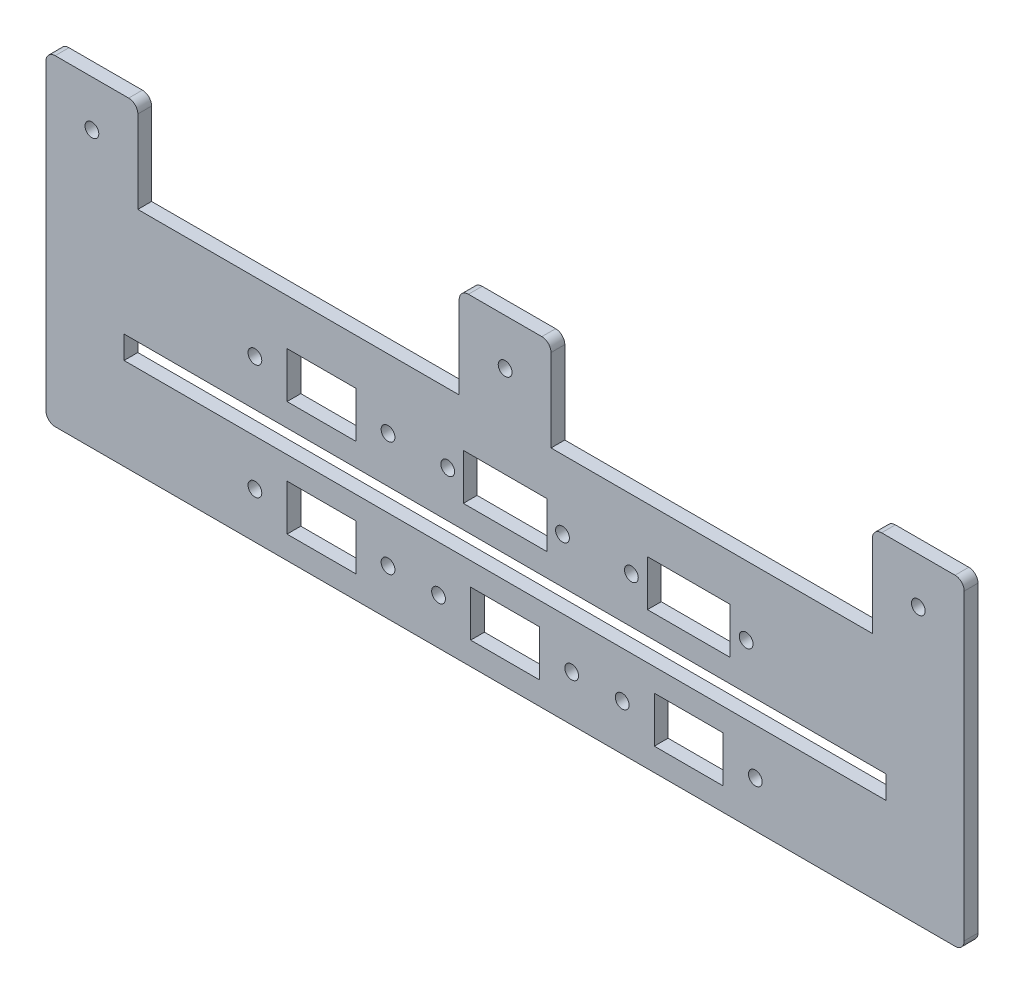
SolidWorks part; units mm, degrees
material "ｱｸﾘﾙ (中-上級の耐衝撃性)"
ref_plane "正面" through (0, 0, 0) normal (0, 0, 1) x (1, 0, 0)
ref_plane "平面" through (0, 0, 0) normal (0, 1, 0) x (1, 0, 0)
ref_plane "右側面" through (0, 0, 0) normal (1, 0, 0) x (0, 0, -1)
sketch "ｽｹｯﾁ1" plane through (0, 0, 0) normal (0, 0, 1) x (1, 0, 0)
  line L1 (-100, 35) -> (100, 35)
  line L2 (-100, 35) -> (-100, -35)
  line L3 (-100, -35) -> (100, -35)
  line L4 (100, 35) -> (100, -35)
  line L5 (-100, 35) -> (100, -35) construction
  line L6 (-100, -35) -> (100, 35) construction
  point P0 (0, 0)
  dimension "D1" = 200
  dimension "D2" = 70
extrude "ﾎﾞｽ - 押し出し1" add sketch "ｽｹｯﾁ1" along normal blind 3
sketch "ｽｹｯﾁ2" plane through (0, 0, 3) normal (0, 0, 1) x (1, 0, 0)
  line L0 (-100, 35) -> (-80, 35)
  line L1 (100, 35) -> (-100, 35) construction
  line L3 (-80, 35) -> (-10, 35)
  line L4 (-80, 35) -> (-80, 15)
  line L5 (-80, 15) -> (-10, 15)
  line L6 (-10, 35) -> (-10, 15)
  line M2 (100, 35) -> (-100, 35)
  dimension "D1" = 20
  dimension "D2" = 70
  dimension "D3" = 20
extrude "ｶｯﾄ - 押し出し1" cut sketch "ｽｹｯﾁ2" against normal blind 3 contours L6 L4 L5 M2
sketch "ｽｹｯﾁ4" plane through (0, 0, 3) normal (0, 0, 1) x (1, 0, 0)
  line L0 (-10, 35) -> (10, 35)
  line L1 (100, 35) -> (-10, 35) construction
  line L3 (10, 35) -> (80, 35)
  line L4 (10, 35) -> (10, 15)
  line L5 (10, 15) -> (80, 15)
  line L6 (80, 35) -> (80, 15)
  line M1 (100, 35) -> (-10, 35)
  dimension "D1" = 20
  dimension "D2" = 70
  dimension "D3" = 20
extrude "ｶｯﾄ - 押し出し2" cut sketch "ｽｹｯﾁ4" against normal blind 3 contours L6 L4 L5 M1
sketch "ｽｹｯﾁ5" plane through (0, 0, 3) normal (0, 0, 1) x (1, 0, 0)
  line L0 (80, 15) -> (80, -10)
  line L1 (80, -10) -> (83, -10)
  line L2 (-80, 15) -> (-83, 15)
  line L3 (83, -10) -> (-83, -10)
  line L4 (83, -10) -> (83, -15)
  line L5 (83, -15) -> (-83, -15)
  line L6 (-83, -10) -> (-83, -15)
  dimension "D1" = 25
  dimension "D2" = 3
  dimension "D3" = 166
  dimension "D4" = 5
  dimension "D5" = 3
extrude "ｶｯﾄ - 押し出し3" cut sketch "ｽｹｯﾁ5" against normal blind 3 contours L3 L6 L5 L4
sketch "ｽｹｯﾁ6" plane through (0, 0, 3) normal (0, 0, 1) x (1, 0, 0)
  line L0 (-100, -33) -> (-100, 33)
  line L1 (-98, 35) -> (-82, 35)
  line L2 (-80, 33) -> (-80, 17)
  line L3 (-78, 15) -> (-12, 15)
  line L4 (-10, 17) -> (-10, 33)
  line L5 (-8, 35) -> (8, 35)
  line L6 (10, 33) -> (10, 17)
  line L7 (12, 15) -> (78, 15)
  line L8 (80, 17) -> (80, 33)
  line L9 (82, 35) -> (98, 35)
  line L10 (100, 33) -> (100, -33)
  line L11 (98, -35) -> (-98, -35)
  line L12 (-100, -35) -> (-100, 35)
  line L13 (-100, 35) -> (-80, 35)
  line L14 (-80, 35) -> (-80, 15)
  line L15 (-80, 15) -> (-10, 15)
  line L16 (-10, 15) -> (-10, 35)
  line L17 (-10, 35) -> (10, 35)
  line L18 (10, 35) -> (10, 15)
  line L19 (10, 15) -> (80, 15)
  line L20 (80, 15) -> (80, 35)
  line L21 (80, 35) -> (100, 35)
  line L22 (100, 35) -> (100, -35)
  line L23 (100, -35) -> (-100, -35)
  arc A0 (-100, -33) -> (-98, -35) centre (-98, -33) ccw
  arc A1 (98, -35) -> (100, -33) centre (98, -33) ccw
  arc A2 (100, 33) -> (98, 35) centre (98, 33) ccw
  arc A3 (82, 35) -> (80, 33) centre (82, 33) ccw
  arc A4 (80, 17) -> (78, 15) centre (78, 17) cw
  arc A5 (12, 15) -> (10, 17) centre (12, 17) cw
  arc A6 (10, 33) -> (8, 35) centre (8, 33) ccw
  arc A7 (-8, 35) -> (-10, 33) centre (-8, 33) ccw
  arc A8 (-10, 17) -> (-12, 15) centre (-12, 17) cw
  arc A9 (-78, 15) -> (-80, 17) centre (-78, 17) cw
  arc A10 (-80, 33) -> (-82, 35) centre (-82, 33) ccw
  arc A11 (-98, 35) -> (-100, 33) centre (-98, 33) ccw
  point P26 (-100, -35)
  point P29 (100, -35)
  point P32 (100, 35)
  point P35 (80, 35)
  point P38 (80, 15)
  point P41 (10, 15)
  point P44 (10, 35)
  point P47 (-10, 35)
  point P50 (-10, 15)
  point P53 (-80, 15)
  point P56 (-80, 35)
  point P59 (-100, 35)
  line M25 (100, 35) -> (80, 35)
  line M26 (80, 35) -> (80, 15)
  line M28 (10, 15) -> (10, 35)
  line M29 (10, 35) -> (-10, 35)
  line M30 (-10, 35) -> (-10, 15)
  line M32 (-80, 15) -> (-80, 35)
  line M33 (-80, 35) -> (-100, 35)
  line M34 (-100, 35) -> (-100, -35)
  line M35 (-100, -35) -> (100, -35)
  line M36 (100, -35) -> (100, 35)
  dimension "D1" = 2
extrude "ｶｯﾄ - 押し出し8" cut sketch "ｽｹｯﾁ6" against normal blind 3 contours A11 M33 M34 | A10 M32 M33 | A7 M29 M30 | A6 M28 M29 | A3 M25 M26 | A2 M36 M25 | A1 M35 M36 | A0 M34 M35 | L13 L14 L15 L16 L17 L18 L19 L20 L21 L22 L23 L12
sketch "ｽｹｯﾁ7" plane through (0, 0, 3) normal (0, 0, 1) x (1, 0, 0)
  line L1 (-80, 15) -> (-90, 15)
  line L2 (-80, 15) -> (-80, 25)
  line L3 (-80, 25) -> (-90, 25)
  line L4 (-90, 15) -> (-90, 25)
  line L5 (-10, 15) -> (0, 15)
  line L6 (-10, 15) -> (-10, 25)
  line L7 (-10, 25) -> (0, 25)
  line L8 (0, 15) -> (0, 25)
  line L9 (80, 15) -> (90, 15)
  line L10 (80, 15) -> (80, 25)
  line L11 (80, 25) -> (90, 25)
  line L12 (90, 15) -> (90, 25)
  circle A0 centre (-90, 25) radius 1.5
  circle A1 centre (0, 25) radius 1.5
  circle A2 centre (90, 25) radius 1.5
  dimension "D3" = 3
  dimension "D8" = 3
  dimension "D9" = 3
  dimension "D1" = 10
  dimension "D2" = 10
  dimension "D4" = 10
  dimension "D5" = 10
  dimension "D6" = 10
  dimension "D7" = 10
extrude "ｶｯﾄ - 押し出し9" cut sketch "ｽｹｯﾁ7" against normal blind 3 contours A0 | A1 | A2
sketch "ｽｹｯﾁ8" plane through (0, 0, 3) normal (0, 0, 1) x (1, 0, 0)
  line L0 (83, -15) -> (83, -20)
  line L1 (83, -20) -> (47.5, -20)
  line L2 (32.5, -20) -> (7.5, -20)
  line L3 (47.5, -20) -> (32.5, -20)
  line L4 (47.5, -20) -> (47.5, -30)
  line L5 (47.5, -30) -> (32.5, -30)
  line L6 (32.5, -20) -> (32.5, -30)
  line L7 (0, 25) -> (0, -26.1678)
  line L8 (7.5, -20) -> (-7.5, -20)
  line L9 (7.5, -20) -> (7.5, -30)
  line L10 (7.5, -30) -> (-7.5, -30)
  line L11 (-7.5, -20) -> (-7.5, -30)
  line L12 (-7.5, -20) -> (-32.5, -20)
  line L14 (-32.5, -20) -> (-47.5, -20)
  line L15 (-32.5, -20) -> (-32.5, -30)
  line L16 (-32.5, -30) -> (-47.5, -30)
  line L17 (-47.5, -20) -> (-47.5, -30)
  dimension "D1" = 5
  dimension "D2" = 35.5
  dimension "D3" = 15
  dimension "D4" = 10
  dimension "D5" = 25
  dimension "D6" = 15
  dimension "D7" = 10
  dimension "D8" = 25
  dimension "D9" = 15
  dimension "D10" = 10
extrude "ｶｯﾄ - 押し出し10" cut sketch "ｽｹｯﾁ8" against normal blind 3
sketch "ｽｹｯﾁ9" plane through (0, 0, 3) normal (0, 0, 1) x (1, 0, 0)
  line L0 (-47.5, -20) -> (-47.5, -15)
  line L1 (83, -15) -> (-83, -15) construction
  line L2 (-47.5, -15) -> (-47.5, -10)
  line L3 (83, -10) -> (-83, -10) construction
  line L4 (-47.5, -10) -> (-47.5, -5)
  line L5 (40, -20) -> (40, -5)
  line L6 (-47.5, -5) -> (-32.5, -5)
  line L7 (-47.5, -5) -> (-47.5, 5)
  line L8 (-47.5, 5) -> (-32.5, 5)
  line L9 (-32.5, -5) -> (-32.5, 5)
  line L10 (47.5, -20) -> (32.5, -20) construction
  line L11 (40, -5) -> (31, -5)
  line L12 (0, 0) -> (0, -5)
  line L13 (31, -5) -> (49, -5)
  line L14 (31, -5) -> (31, 5)
  line L15 (31, 5) -> (49, 5)
  line L16 (49, -5) -> (49, 5)
  line L17 (9.1, -5) -> (0, -5)
  line L19 (9.1, -5) -> (-9.1, -5)
  line L20 (9.1, -5) -> (9.1, 5)
  line L21 (9.1, 5) -> (-9.1, 5)
  line L22 (-9.1, -5) -> (-9.1, 5)
  dimension "D1" = 5
  dimension "D2" = 15
  dimension "D3" = 10
  dimension "D4" = 9
  dimension "D5" = 18
  dimension "D6" = 9.1
  dimension "D7" = 18.2
extrude "ｶｯﾄ - 押し出し11" cut sketch "ｽｹｯﾁ9" against normal blind 3
sketch "ｽｹｯﾁ10" plane through (0, 0, 3) normal (0, 0, 1) x (1, 0, 0)
  line L0 (0, 0) -> (12.5, 0)
  line L1 (0, 0) -> (-12.5, 0)
  line L2 (40, -5) -> (40, 0)
  line L3 (31, -5) -> (49, -5) construction
  line L4 (40, 0) -> (52.5, 0)
  line L5 (40, 0) -> (27.5, 0)
  line L6 (-40, 5) -> (-40, 0)
  line L7 (-47.5, 5) -> (-32.5, 5) construction
  line L8 (-40, -30) -> (-40, -20)
  line L9 (-32.5, -20) -> (-47.5, -20) construction
  line L10 (-32.5, -30) -> (-47.5, -30) construction
  line L11 (0, -30) -> (0, -20)
  line L12 (7.5, -30) -> (-7.5, -30) construction
  line L13 (7.5, -20) -> (-7.5, -20) construction
  line L14 (40, -30) -> (40, -20)
  line L15 (47.5, -30) -> (32.5, -30) construction
  line L16 (47.5, -20) -> (32.5, -20) construction
  line L17 (40, -25) -> (54.5, -25)
  line L18 (40, -25) -> (25.5, -25)
  line L19 (0, -25) -> (14.5, -25)
  line L20 (0, -25) -> (-14.5, -25)
  line L21 (-40, -25) -> (-25.5, -25)
  line L22 (-40, -25) -> (-54.5, -25)
  line L23 (-40, 0) -> (-25.5, 0)
  line L24 (-40, 0) -> (-54.5, 0)
  circle A0 centre (-54.5, 0) radius 1.5
  circle A1 centre (-25.5, 0) radius 1.5
  circle A2 centre (-12.5, 0) radius 1.5
  circle A3 centre (12.5, 0) radius 1.5
  circle A4 centre (27.5, 0) radius 1.5
  circle A5 centre (52.5, 0) radius 1.5
  circle A6 centre (54.5, -25) radius 1.5
  circle A7 centre (25.5, -25) radius 1.5
  circle A8 centre (14.5, -25) radius 1.5
  circle A9 centre (-14.5, -25) radius 1.5
  circle A10 centre (-25.5, -25) radius 1.5
  circle A11 centre (-54.5, -25) radius 1.5
  dimension "D13" = 3
  dimension "D14" = 3
  dimension "D15" = 3
  dimension "D16" = 3
  dimension "D17" = 3
  dimension "D18" = 3
  dimension "D19" = 3
  dimension "D20" = 3
  dimension "D21" = 3
  dimension "D22" = 3
  dimension "D23" = 3
  dimension "D24" = 3
  dimension "D1" = 12.5
  dimension "D2" = 12.5
  dimension "D3" = 12.5
  dimension "D4" = 12.5
  dimension "D5" = 14.5
  dimension "D6" = 14.5
  dimension "D7" = 14.5
  dimension "D8" = 14.5
  dimension "D9" = 14.5
  dimension "D10" = 14.5
  dimension "D11" = 14.5
  dimension "D12" = 14.5
extrude "ｶｯﾄ - 押し出し12" cut sketch "ｽｹｯﾁ10" against normal blind 3 contours A0 | A2 | A1 | A3 | A4 | A5 | A6 | A7 | A8 | A9 | A10 | A11
